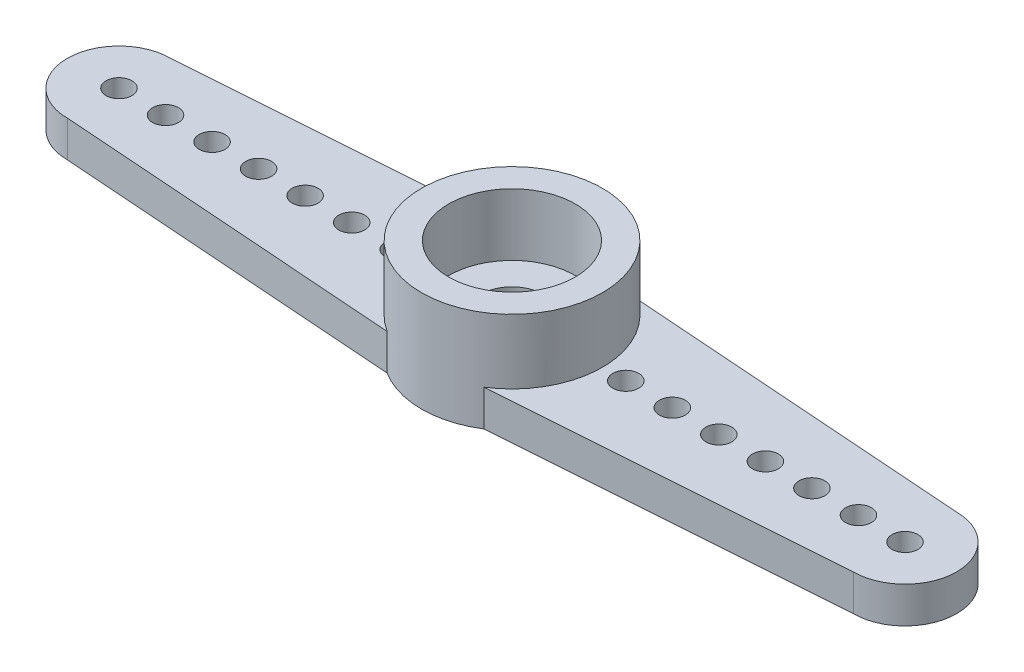
SolidWorks part; units mm, degrees
other "Camera1"
material "ABS"
ref_plane "Front Plane" through (0, 0, 0) normal (0, 0, 1) x (1, 0, 0)
ref_plane "Top Plane" through (0, 0, 0) normal (0, 1, 0) x (1, 0, 0)
ref_plane "Right Plane" through (0, 0, 0) normal (1, 0, 0) x (0, 0, -1)
sketch "Sketch1" plane through (0, 0, 0) normal (0, 1, 0) x (1, 0, 0)
  line L0 (-17.2, 0) -> (17.2, 0) construction
  line L1 (0, -8.35) -> (0, 8.35) construction
  line L2 (-15.2, 2) -> (-2, 2.95)
  line L3 (-15.2, -2) -> (-2, -2.95)
  line L4 (2, 6.35) -> (2, 3.5)
  line L5 (-2, 6.35) -> (-2, 2.95)
  line L6 (2, -6.35) -> (2, -3.5)
  line L7 (-2, -6.35) -> (-2, -2.95)
  line L8 (15.2, 2) -> (2, 3.5)
  line L9 (15.2, -2) -> (2, -3.5)
  circle A0 centre (0, 0) radius 3.5 construction
  arc A1 (-15.2, 2) -> (-15.2, -2) centre (-15.2, 0) ccw
  arc A2 (15.2, 2) -> (15.2, -2) centre (15.2, 0) cw
  arc A3 (2, 6.35) -> (-2, 6.35) centre (0, 6.35) ccw
  circle A4 centre (0, 6.35) radius 0.5
  circle A5 centre (0, 4.55) radius 0.5
  circle A6 centre (0, -4.55) radius 0.5
  circle A7 centre (0, -6.35) radius 0.5
  arc A8 (2, -6.35) -> (-2, -6.35) centre (0, -6.35) cw
  circle A10 centre (-15.2, 0) radius 0.5
  circle A11 centre (15.2, 0) radius 0.5
  circle A12 centre (-13.4, 0) radius 0.5
  circle A13 centre (-11.6, 0) radius 0.5
  circle A14 centre (-9.8, 0) radius 0.5
  circle A15 centre (-8, 0) radius 0.5
  circle A16 centre (-6.2, 0) radius 0.5
  circle A17 centre (-4.4, 0) radius 0.5
  circle A18 centre (13.4, 0) radius 0.5
  circle A19 centre (11.6, 0) radius 0.5
  circle A20 centre (9.8, 0) radius 0.5
  circle A21 centre (8, 0) radius 0.5
  circle A22 centre (6.2, 0) radius 0.5
  circle A23 centre (4.4, 0) radius 0.5
  point P5 (0, 0)
  point P8 (0, 0)
  point P25 (0, 6.85)
  point P26 (0, 4.05)
  dimension "D1" = 7
  dimension "D4" = 4
  dimension "D6" = 1
  dimension "D2" = 34.4
  dimension "D3" = 16.7
  dimension "D5" = 2
  dimension "D7" = 2.8
  dimension "D8" = 7
  dimension "D10" = 5.9
  dimension "D11" = 7
  dimension "D12" = 7
extrude "Boss-Extrude1" add sketch "Sketch1" along normal blind 1.4
sketch "Sketch2" plane through (0, 0, 0) normal (0, -1, 0) x (1, 0, 0)
  circle A0 centre (0, 0) radius 2.35
  dimension "D1" = 4.7
extrude "Cut-Extrude1" cut sketch "Sketch2" against normal blind 1
sketch "Sketch3" plane through (0, 1.4, 0) normal (0, 1, 0) x (1, 0, 0)
  circle A0 centre (0, 0) radius 2.45
  circle A1 centre (0, 0) radius 3.5
  dimension "D1" = 4.9
  dimension "D2" = 7
extrude "Boss-Extrude2" add sketch "Sketch3" along normal blind 2.5
sketch "Sketch4" plane through (0, 1.4, 0) normal (0, 1, 0) x (1, 0, 0)
  circle A0 centre (0, 0) radius 1.2
  dimension "D1" = 2.4
extrude "Cut-Extrude2" cut sketch "Sketch4" against normal through all
sketch "Sketch5" plane through (0, 1.4, 0) normal (0, 1, 0) x (1, 0, 0)
  circle A0 centre (0, 0) radius 1.2 construction
  circle A1 centre (0, 0) radius 2.45
  circle A2 centre (0, 0) radius 2.45
  circle A3 centre (0, 0) radius 1.2
  dimension "D1" = 0
extrude "Boss-Extrude3" add sketch "Sketch5" along normal blind 0.1
sketch "Sketch6" plane through (0, 0, 0) normal (0, -1, 0) x (1, 0, 0)
  line L0 (-2, -2.95) -> (-15.2, -2) construction
  line L1 (-1.8686, -2.9595) -> (-15.2, -2)
  line L2 (-15.2, 2) -> (-2, 2.95) construction
  line L3 (-15.2, 2) -> (-1.8686, 2.9595)
  line L4 (0, -9.3016) -> (0, 8.6978) construction
  line L5 (1.8686, -2.9595) -> (15.2, -2)
  line L6 (15.2, 2) -> (1.8686, 2.9595)
  line L8 (-17.8676, -8.836) -> (17.8676, -8.836)
  line L9 (-17.8676, -8.836) -> (-17.8676, 8.836)
  line L10 (-17.8676, 8.836) -> (17.8676, 8.836)
  line L11 (17.8676, -8.836) -> (17.8676, 8.836)
  line L12 (-17.8676, -8.836) -> (17.8676, 8.836) construction
  line L13 (-17.8676, 8.836) -> (17.8676, -8.836) construction
  arc A0 (-15.2, 2) -> (-15.2, -2) centre (-15.2, 0) ccw construction
  arc A1 (-15.2, 2) -> (-15.2, -2) centre (-15.2, 0) ccw
  circle A2 centre (0, 0) radius 3.5 construction
  arc A3 (1.8686, 2.9595) -> (-1.8686, 2.9595) centre (0, 0) ccw
  arc A4 (15.2, 2) -> (15.2, -2) centre (15.2, 0) cw
  arc A5 (-1.8686, -2.9595) -> (1.8686, -2.9595) centre (0, 0) ccw
extrude "Cut-Extrude4" cut sketch "Sketch6" against normal through all
sketch "Sketch7" [suppressed] plane through (0, 0, 0) normal (0, -1, 0) x (1, 0, 0)
  line L0 (0, 3.5) -> (-17.7318, 3.5)
  line L1 (-17.7318, 3.5) -> (-17.7318, -3.5)
  line L2 (-17.7318, -3.5) -> (0, -3.5)
  circle A0 centre (0, 0) radius 3.5 construction
  arc A1 (0, 3.5) -> (0, -3.5) centre (0, 0) ccw
extrude "Cut-Extrude5" [suppressed] cut sketch "Sketch7" against normal through all
